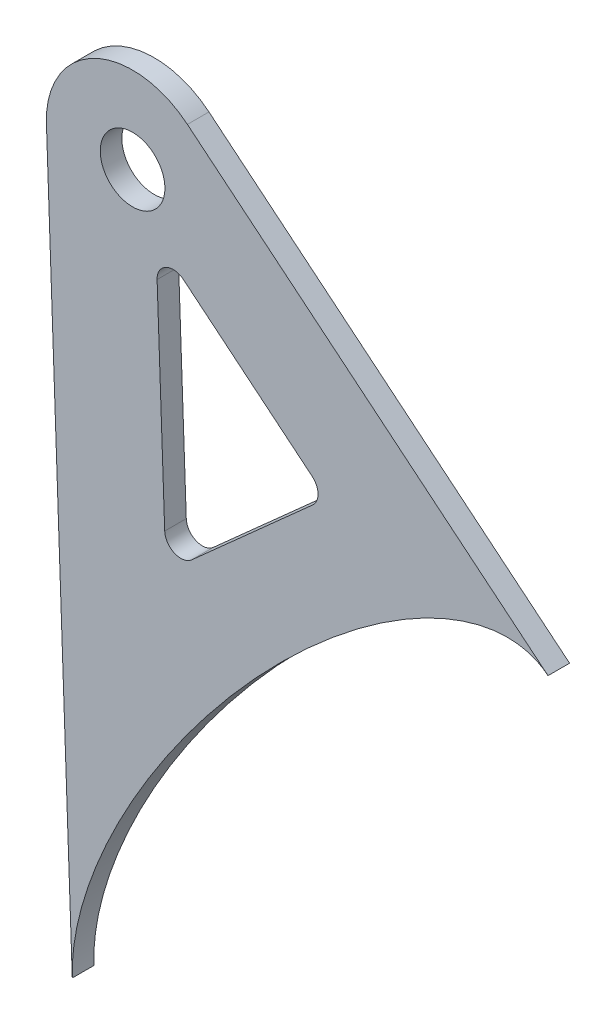
SolidWorks part; units mm, degrees
material "Stal węglowa"
ref_plane "Płaszczyzna XY" through (0, 0, 0) normal (0, 0, 1) x (1, 0, 0)
ref_plane "Płaszczyzna XZ" through (0, 0, 0) normal (0, 1, 0) x (1, 0, 0)
ref_plane "Płaszczyzna YZ" through (0, 0, 0) normal (1, 0, 0) x (0, 0, -1)
sketch "Szkic1" plane through (0, 0, 432.28) normal (0, 0, 1) x (1, 0, 0)
  line L0 (1364.7278, -206.4864) -> (1376.6634, -216.3198)
  line L1 (1362.2749, -207.6974) -> (1362.9809, -227.5576)
  line L2 (1352.0051, -200.2842) -> (1354.4039, -267.7623)
  line L3 (1365.0869, -193.8256) -> (1398.5485, -221.3936)
  line L4 (1376.7087, -218.5964) -> (1365.479, -228.6232)
  line L6 (1362.1565, -204.3681) -> (1364.3976, -267.4071) construction
  line L8 (1362.1565, -204.3681) -> (1392.1899, -229.1116) construction
  circle A0 centre (1360, -200) radius 3
  arc A1 (1365.0869, -193.8256) -> (1352.0051, -200.2842) centre (1360, -200) ccw
  circle A2 centre (1360, -200) radius 8 construction
  arc A3 (1376.7087, -218.5964) -> (1376.6634, -216.3198) centre (1375.7096, -217.4775) ccw
  arc A4 (1364.7278, -206.4864) -> (1362.2749, -207.6974) centre (1363.774, -207.6441) ccw
  arc A5 (1362.1565, -204.3681) -> (1362.1565, -204.3681) centre (1362.1565, -204.3681) ccw construction
  arc A6 (1365.479, -228.6232) -> (1362.9809, -227.5576) centre (1364.48, -227.5043) cw
  spline S1 degree 3 poles (1354.4039, -267.7623) (1353.4325, -240.4367) (1386.5371, -211.615) (1398.5273, -221.3762) (1398.5344, -221.382) (1398.5414, -221.3878) (1398.5485, -221.3936) knots 0.085288 0.085288 0.085288 0.085288 0.5 0.5 0.5 0.500549 0.500549 0.500549 0.500549 weights 0.717042 0.352731 0.44705 1 0.999268 0.998537 0.997806
  spline S3 degree 3 poles (1356.5249, 272.9701) (1375.9126, 288.7536) (1417.915, 237.1596) (1398.5273, 221.3762) (1379.1396, 205.5928) (1337.1372, 257.1867) (1356.5249, 272.9701) (1375.9126, 288.7536) (1417.915, 237.1596) knots -0.5 0 0 0 0.5 0.5 0.5 1 1 1 1.5 1.5 1.5 weights 1 0.333333 0.333333 1 0.333333 0.333333 1 0.333333 0.333333 only from (1356.5249, 272.9701) to (1356.5249, 272.9701)
  point P21 (1378.013, -217.4318)
  point P24 (1363.0945, -230.7523)
  dimension "D1" = 6
  dimension "D5" = 1.5
  dimension "D2" = 10
  dimension "D3" = 25
  dimension "D4" = 20
extrude "Dodanie-wyciągnięcie1" add sketch "Szkic1" along normal blind 2 contours L4 L0 L1 | A0 | S1 L3 A1 L2
